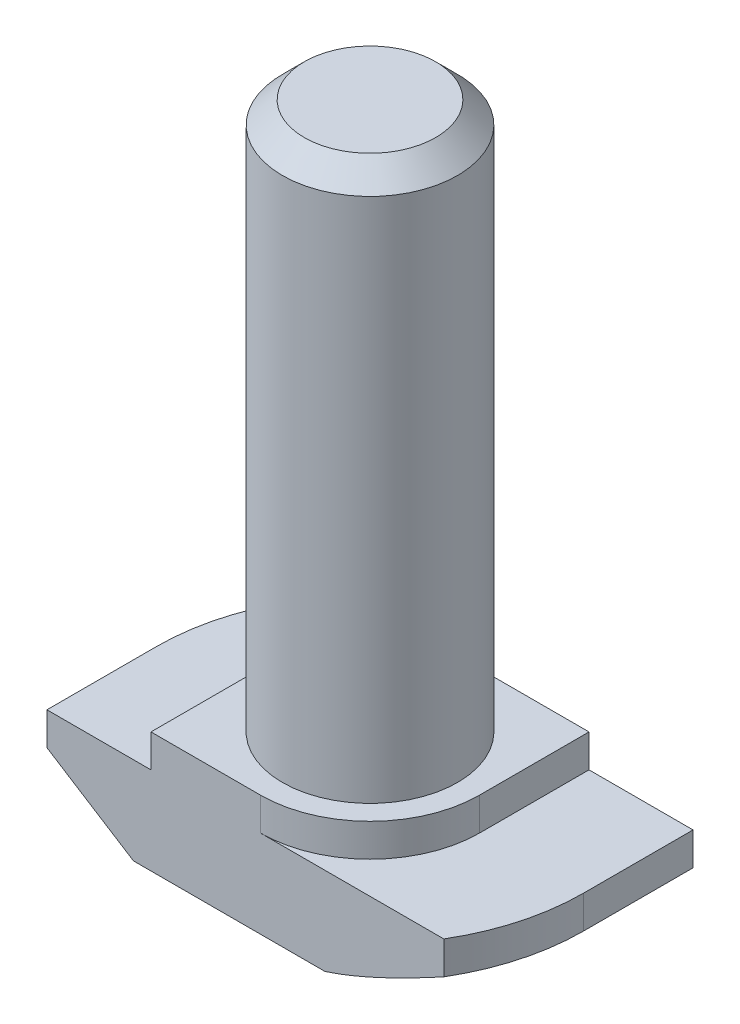
SolidWorks part; units mm, degrees
ref_plane "Спереди" through (0, 0, 0) normal (0, 0, 1) x (1, 0, 0)
ref_plane "Сверху" through (0, 0, 0) normal (0, 1, 0) x (1, 0, 0)
ref_plane "Справа" through (0, 0, 0) normal (1, 0, 0) x (0, 0, -1)
sketch "Эскиз1" plane through (0, 0, 0) normal (0, 0, 1) x (1, 0, 0)
  line L0 (9.75, 0) -> (-9.75, 0)
  line L1 (-9.75, 0) -> (-9.75, 4)
  line L2 (-9.75, 4) -> (-5, 4)
  line L3 (-5, 4) -> (-5, 5.5)
  line L4 (-5, 5.5) -> (5, 5.5)
  line L5 (0, 5.5) -> (0, 0) construction
  line L6 (5, 4) -> (5, 5.5)
  line L7 (9.75, 4) -> (5, 4)
  line L8 (9.75, 0) -> (9.75, 4)
  point P12 (-8.25, 2.6435)
  point P13 (-4, 3.6993)
  dimension "D1" = 10
  dimension "D2" = 19.5
  dimension "D3" = 5.5
  dimension "D4" = 1.5
extrude "Бобышка-Вытянуть1" add sketch "Эскиз1" along normal mid plane 10
sketch "Эскиз3" plane through (0, 5.5, 0) normal (0, 1, 0) x (1, 0, 0)
  line L1 (5, 5) -> (-5, 5) construction
  line L2 (-5, 0) -> (-5, 5)
  line L3 (-5, 5) -> (0, 5)
  line L4 (0, -5) -> (5, -5)
  line L5 (5, -5) -> (-5, -5) construction
  line L6 (5, -5) -> (5, 0)
  line L7 (5, -5) -> (5, 5) construction
  arc A0 (-5, 0) -> (0, 5) centre (0, 0) cw
  arc A1 (5, 0) -> (0, -5) centre (0, 0) cw
extrude "Вырез-Вытянуть1" cut sketch "Эскиз3" against normal up to surface (1.5 mm away) up to face at (-7.375, 4, 0)
sketch "Эскиз2" plane through (0, 5.5, 0) normal (0, 1, 0) x (1, 0, 0)
  circle A0 centre (0, 0) radius 4
  dimension "D1" = 8
extrude "Бобышка-Вытянуть2" add sketch "Эскиз2" along normal blind 25
cosmetic thread "Условное изображение резьбы1" parameters "D1"=25, "D2"=6.619
sketch "Эскиз4" plane through (0, 4, 0) normal (0, 1, 0) x (1, 0, 0)
  line L0 (-9.75, -5) -> (-9.75, 5) construction
  line L1 (9.75, -5) -> (9.75, 5) construction
  line L2 (-8.3703, 5) -> (-9.75, 5)
  line L3 (-9.75, 5) -> (-9.75, 0)
  line L4 (8.3703, -5) -> (9.75, -5)
  line L5 (9.75, -5) -> (9.75, 0)
  arc A0 (-9.75, 0) -> (-8.3703, 5) centre (0, 0) cw
  arc A1 (9.75, 0) -> (8.3703, -5) centre (0, 0) cw
extrude "Вырез-Вытянуть2" cut sketch "Эскиз4" against normal through all
sketch "Эскиз5" plane through (0, 0, 5) normal (0, 0, 1) x (1, 0, 0)
  line L0 (-9.75, 2.5) -> (-5.8, 0)
  line L1 (-9.75, 4) -> (-9.75, 0) construction
  line L2 (-9.75, 0) -> (8.3703, 0) construction
  line L3 (-5.8, 0) -> (-9.75, 0)
  line L4 (-9.75, 0) -> (-9.75, 2.5)
  line L6 (-5, 4) -> (-9.75, 4) construction
  line L7 (-5, 5.5) -> (-5, 4) construction
  point P6 (-4.9519, 0)
  point P9 (0, 0)
  point P10 (-4.6154, 0)
  point P12 (-8.25, 2.2665)
  point P15 (0, 0)
  dimension "D1" = 1.5
  dimension "D2" = 0.8
sketch "Эскиз6" plane through (0, 0, 0) normal (0, -1, 0) x (1, 0, 0)
  line L0 (0, -9.75) -> (9.75, -9.75)
  line L1 (9.75, -9.75) -> (9.75, 0)
  line L2 (0, 9.75) -> (-9.75, 9.75)
  line L3 (-9.75, 9.75) -> (-9.75, 0)
  arc A0 (-9.75, 0) -> (0, -9.75) centre (0, 0) ccw
  arc A1 (9.75, 0) -> (0, 9.75) centre (0, 0) ccw
  point P10 (0, 0)
sweep "Вырез-По траектории1" cut profiles "Эскиз5" path "Эскиз6"
chamfer "Фаска2" distance 1 angle 45 1 edges at (0, 30.5, 4)
